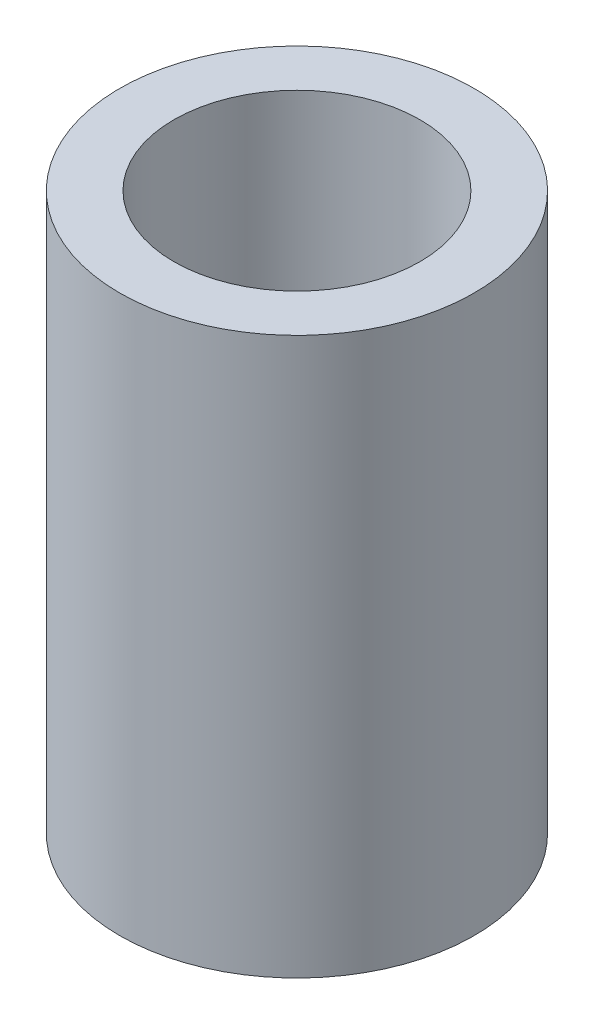
SolidWorks part; units mm, degrees
ref_plane "Front Plane" through (0, 0, 0) normal (0, 0, 1) x (1, 0, 0)
ref_plane "Top Plane" through (0, 0, 0) normal (0, 1, 0) x (1, 0, 0)
ref_plane "Right Plane" through (0, 0, 0) normal (1, 0, 0) x (0, 0, -1)
sketch "Sketch1" plane through (0, 0, 0) normal (0, 1, 0) x (1, 0, 0)
  circle A0 centre (0, 0) radius 2.1
  circle A1 centre (0, 0) radius 3.025
  dimension "D1" = 4.2
  dimension "D2" = 6.05
extrude "Boss-Extrude1" add sketch "Sketch1" along normal blind 9.5
